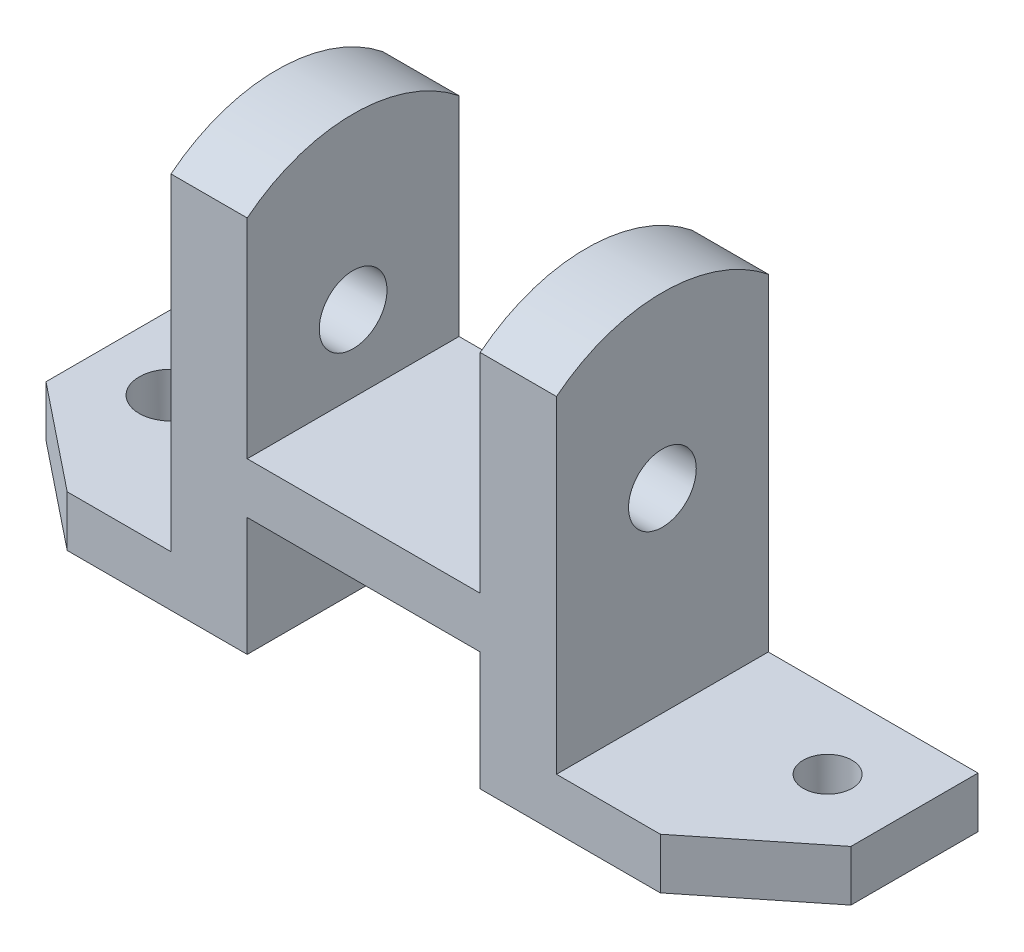
SolidWorks part; units mm, degrees
ref_plane "Front Plane" through (0, 0, 0) normal (0, 0, 1) x (1, 0, 0)
ref_plane "Top Plane" through (0, 0, 0) normal (0, 1, 0) x (1, 0, 0)
ref_plane "Right Plane" through (0, 0, 0) normal (1, 0, 0) x (0, 0, -1)
sketch "Sketch1" plane through (0, 0, 0) normal (0, 1, 0) x (1, 0, 0)
  line L1 (-45.5, 25) -> (45.5, 25)
  line L2 (-45.5, 25) -> (-45.5, -25)
  line L3 (-45.5, -25) -> (45.5, -25)
  line L4 (45.5, 25) -> (45.5, -25)
  line L5 (-45.5, 25) -> (45.5, -25) construction
  line L6 (-45.5, -25) -> (45.5, 25) construction
  point P0 (0, 0)
  dimension "D1" = 91
  dimension "D2" = 50
extrude "Boss-Extrude1" add sketch "Sketch1" against normal blind 12
sketch "Sketch2" plane through (0, -12, 0) normal (0, -1, 0) x (1, 0, 0)
  line L0 (45.5, -25) -> (-45.5, -25) construction
  line L1 (-45.5, 25) -> (-27.5, 25)
  line L2 (-45.5, 25) -> (-45.5, -25)
  line L3 (-45.5, -25) -> (-27.5, -25)
  line L4 (-27.5, 25) -> (-27.5, -25)
  line L6 (45.5, 25) -> (27.5, 25)
  line L7 (45.5, 25) -> (45.5, -25)
  line L8 (45.5, -25) -> (27.5, -25)
  line L9 (27.5, 25) -> (27.5, -25)
  dimension "D1" = 18
  dimension "D2" = 18
extrude "Boss-Extrude2" add sketch "Sketch2" along normal blind 28
sketch "Sketch4" plane through (45.5, 0, 0) normal (1, 0, 0) x (0, 0, -1)
  line L0 (25, -40) -> (25, 0) construction
  line L1 (-25, -40) -> (25, -40)
  line L2 (-25, -40) -> (-25, -28)
  line L3 (-25, -28) -> (25, -28)
  line L4 (25, -40) -> (25, -28)
  dimension "D1" = 12
extrude "Boss-Extrude3" add sketch "Sketch4" along normal blind 49.5
sketch "Sketch5" plane through (-45.5, 0, 0) normal (-1, 0, 0) x (0, 0, 1)
  line L0 (25, -40) -> (25, 0) construction
  line L1 (-25, -40) -> (25, -40)
  line L2 (-25, -40) -> (-25, -28)
  line L3 (-25, -28) -> (25, -28)
  line L4 (25, -40) -> (25, -28)
  dimension "D1" = 12
extrude "Boss-Extrude4" add sketch "Sketch5" along normal blind 49.5
sketch "Sketch7" plane through (0, -28, 0) normal (0, 1, 0) x (1, 0, 0)
  line L0 (95, -25) -> (95, -5)
  line L1 (95, 25) -> (95, -25) construction
  line L2 (95, -5) -> (70, -25)
  line L3 (95, -25) -> (45.5, -25) construction
  line L4 (70, -25) -> (95, -25)
  dimension "D1" = 25
  dimension "D2" = 20
extrude "Cut-Extrude1" cut sketch "Sketch7" against normal through all both
sketch "Sketch8" plane through (0, -28, 0) normal (0, 1, 0) x (1, 0, 0)
  line L0 (-95, -25) -> (-95, -5)
  line L1 (-95, -25) -> (-95, 25) construction
  line L2 (-95, -5) -> (-70, -25)
  line L3 (-95, -25) -> (-45.5, -25) construction
  line L4 (-70, -25) -> (-95, -25)
  dimension "D1" = 20
  dimension "D2" = 25
extrude "Cut-Extrude2" cut sketch "Sketch8" against normal through all both
sketch "Sketch9" plane through (0, 0, 0) normal (0, 1, 0) x (1, 0, 0)
  line L0 (-45.5, -25) -> (45.5, -25) construction
  line L1 (-45.5, 25) -> (-27.5, 25)
  line L2 (-45.5, 25) -> (-45.5, -25)
  line L3 (-45.5, -25) -> (-27.5, -25)
  line L4 (-27.5, 25) -> (-27.5, -25)
  line L6 (45.5, 25) -> (27.5, 25)
  line L7 (45.5, 25) -> (45.5, -25)
  line L8 (45.5, -25) -> (27.5, -25)
  line L9 (27.5, 25) -> (27.5, -25)
  dimension "D1" = 18
  dimension "D2" = 18
extrude "Boss-Extrude5" add sketch "Sketch9" along normal blind 58
sketch "Sketch10" plane through (45.5, 0, 0) normal (1, 0, 0) x (0, 0, -1)
  line L0 (-25, 58) -> (25, 58) construction
  line L1 (-25, 49.225) -> (-25, 58)
  line L2 (-25, -28) -> (-25, 58) construction
  line L3 (-25, 58) -> (25, 58)
  line L4 (25, 58) -> (25, 49.225)
  line L5 (25, -28) -> (25, 58) construction
  circle A0 centre (0, 18) radius 8
  arc A1 (25, 49.225) -> (-25, 49.225) centre (0, 18) ccw
  line M4 (25, -28) -> (25, 58)
  line M5 (25, 58) -> (-25, 58)
  line M6 (-25, 58) -> (-25, -28)
  dimension "D2" = 16
  dimension "D3" = 80
  dimension "D1" = 40
extrude "Cut-Extrude3" cut sketch "Sketch10" against normal through all both contours A1 M4 M5 | A1 L3 M6 | A0
sketch "Sketch12" plane through (0, 0, 0) normal (0, 1, 0) x (1, 0, 0)
  line L0 (-77.5, 7) -> (77.5, 7) construction
  line L1 (-95, 25) -> (-45.5, 25) construction
  circle A0 centre (77.5, 7) radius 5.7691
  circle A1 centre (-77.5, 7) radius 7.5
  point P7 (0, 7)
  dimension "D1" = 15
  dimension "D2" = 11.5381
  dimension "D3" = 155
  dimension "D4" = 18
extrude "Cut-Extrude4" cut sketch "Sketch12" against normal through all both
sketch "Sketch15" plane through (0, -12, 0) normal (0, -1, 0) x (1, 0, 0)
  line L0 (-27.5, -25) -> (-27.5, 25) construction
  line L1 (-27.5, -11) -> (27.5, -11)
  line L2 (-27.5, -11) -> (-27.5, -3)
  line L3 (-27.5, -3) -> (27.5, -3)
  line L4 (27.5, -11) -> (27.5, -3)
  line L5 (27.5, 25) -> (27.5, -25) construction
  line L6 (27.5, -25) -> (-27.5, -25) construction
  dimension "D1" = 14
  dimension "D2" = 8
extrude "Boss-Extrude6" add sketch "Sketch15" along normal blind 28
